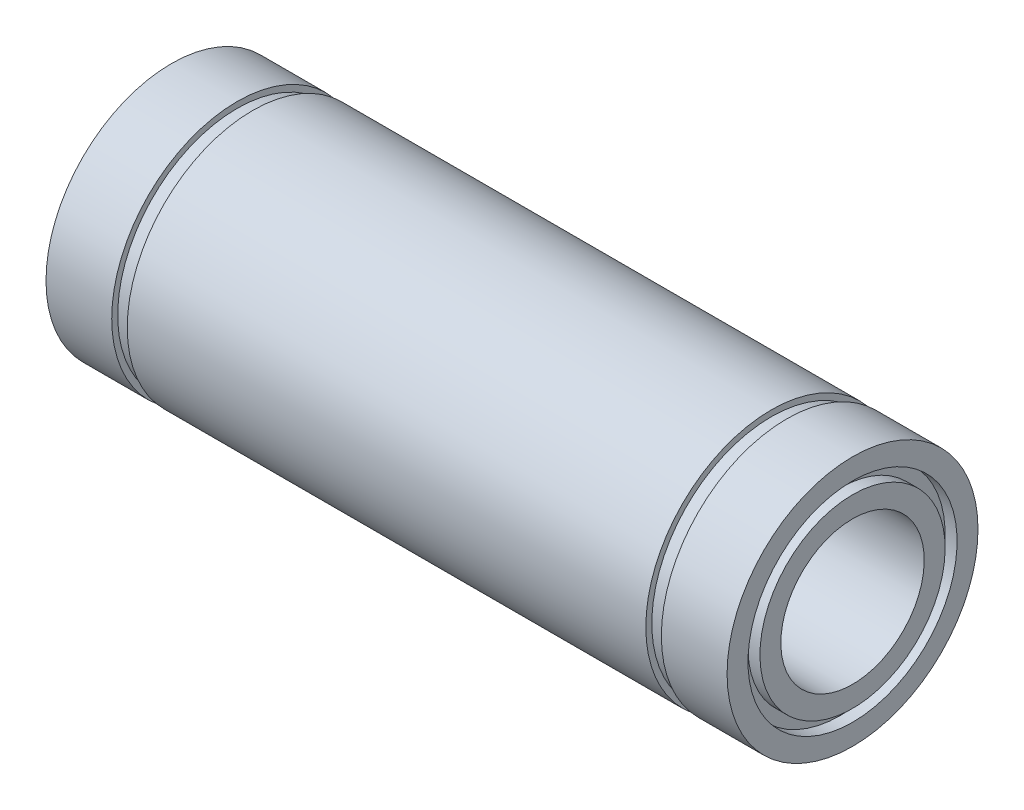
SolidWorks part; units mm, degrees
material "Ст3сп ГОСТ 535-2005"
ref_plane "Plano frontal" through (0, 0, 0) normal (0, 0, 1) x (1, 0, 0)
ref_plane "Plano superior" through (0, 0, 0) normal (0, 1, 0) x (1, 0, 0)
ref_plane "Plano direito" through (0, 0, 0) normal (1, 0, 0) x (0, 0, -1)
sketch "Esboço1" plane through (0, 0, 0) normal (0, 0, 1) x (1, 0, 0)
  line L0 (-28.5, 10.5) -> (-23, 10.5)
  line L1 (-23, 10.5) -> (-23, 10)
  line L2 (-23, 10) -> (-21.7, 10)
  line L3 (-21.7, 10) -> (-21.7, 10.5)
  line L4 (-21.7, 10.5) -> (21.7, 10.5)
  line L5 (21.7, 10.5) -> (21.7, 10)
  line L6 (21.7, 10) -> (23, 10)
  line L7 (23, 10) -> (23, 10.5)
  line L8 (23, 10.5) -> (28.5, 10.5)
  line L9 (28.5, 10.5) -> (28.5, 8.75)
  line L10 (28.5, 6) -> (-28.5, 6)
  line L11 (-28.5, 6) -> (-28.5, 7.75)
  line L12 (0, 6) -> (0, 0) construction
  line L13 (0, 0) -> (-86.5, 0) construction
  line L14 (-28.5, 8.75) -> (-28.5, 10.5)
  line L15 (-28.5, 8.75) -> (-27.5, 8.75)
  line L16 (28.5, 7.75) -> (28.5, 6)
  line L17 (-27.5, 8.75) -> (-27.5, 7.75)
  line L18 (-27.5, 7.75) -> (-28.5, 7.75)
  line L19 (28.5, 8.75) -> (27.5, 8.75)
  line L21 (28.5, 7.75) -> (27.5, 7.75)
  line L22 (27.5, 8.75) -> (27.5, 7.75)
  dimension "D1" = 57
  dimension "D2" = 46
  dimension "D3" = 1.3
  dimension "D4" = 12
  dimension "D5" = 21
  dimension "D6" = 20
  dimension "D7" = 1
  dimension "D8" = 1
  dimension "D9" = 1
  dimension "D10" = 1
revolve "Revolução1" add sketch "Esboço1" angle 360 about L13
